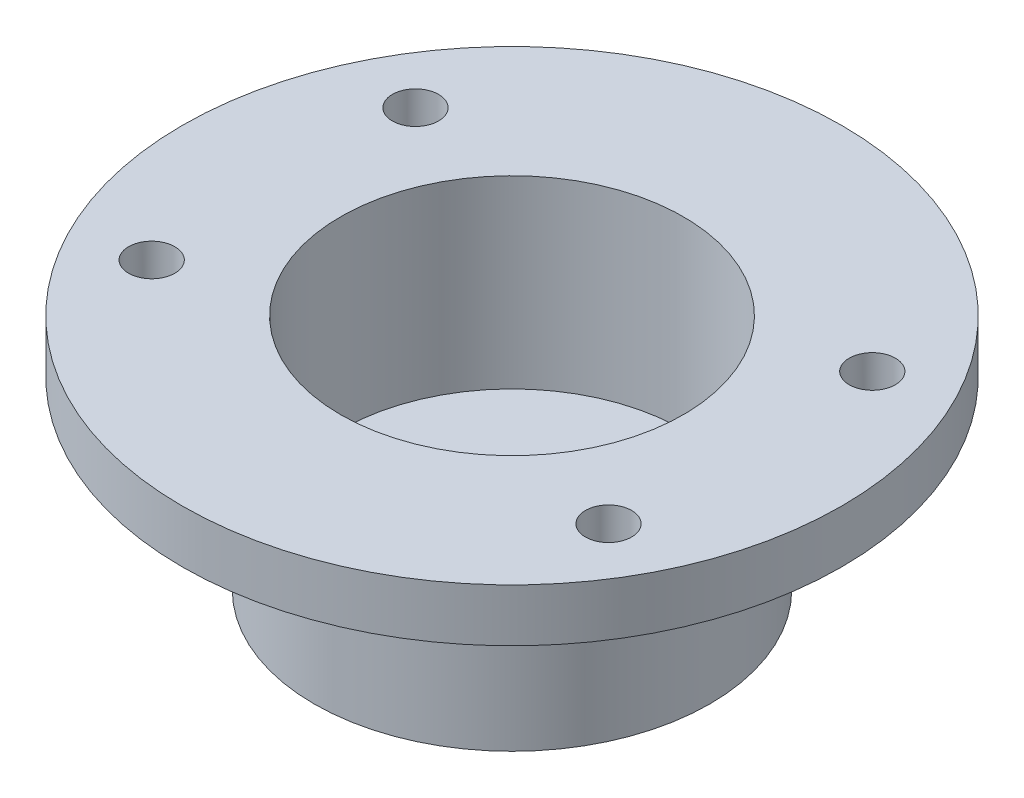
SolidWorks part; units mm, degrees
material "ABS"
ref_plane "Front Plane" through (0, 0, 0) normal (0, 0, 1) x (1, 0, 0)
ref_plane "Top Plane" through (0, 0, 0) normal (0, 1, 0) x (1, 0, 0)
ref_plane "Right Plane" through (0, 0, 0) normal (1, 0, 0) x (0, 0, -1)
sketch "Sketch1" plane through (0, 0, 0) normal (0, 1, 0) x (1, 0, 0)
  circle A0 centre (0, 0) radius 15
  circle A1 centre (0, 0) radius 3
  dimension "D1" = 30
  dimension "D2" = 6
extrude "Boss-Extrude1" add sketch "Sketch1" along normal blind 4
sketch "Sketch2" plane through (0, 4, 0) normal (0, 1, 0) x (1, 0, 0)
  circle A0 centre (0, 0) radius 15 construction
  circle A1 centre (0, 0) radius 15
extrude "Extrude-Thin1" add sketch "Sketch2" along normal blind 10 thin thin type one direction reverse wall 2
sketch "Sketch3" plane through (0, 14, 0) normal (0, 1, 0) x (1, 0, 0)
  circle A0 centre (0, 0) radius 25
  circle A1 centre (0, 0) radius 13 construction
  circle A2 centre (0, 0) radius 13
  dimension "D1" = 50
extrude "Boss-Extrude2" add sketch "Sketch3" along normal blind 4
sketch "Sketch4" plane through (0, 18, 0) normal (0, 1, 0) x (1, 0, 0)
  line L0 (0, 0) -> (-17.3205, 10) construction
  line L1 (0, 0) -> (0, 13) construction
  line L2 (13, 0) -> (-13, 0) construction
  line L3 (0, 0) -> (17.3205, 10) construction
  line L4 (0, 0) -> (17.3205, -10) construction
  line L5 (0, 0) -> (-17.3205, -10) construction
  circle A1 centre (0, 0) radius 13 construction
  circle A3 centre (-17.3205, 10) radius 1.75
  circle A4 centre (0, 0) radius 13 construction
  circle A5 centre (17.3205, 10) radius 1.75
  circle A6 centre (17.3205, -10) radius 1.75
  circle A7 centre (-17.3205, -10) radius 1.75
  point P12 (0, 0)
  dimension "D2" = 20
  dimension "D3" = 3.5
  dimension "D1" = 60
extrude "Cut-Extrude1" cut sketch "Sketch4" against normal up to next
